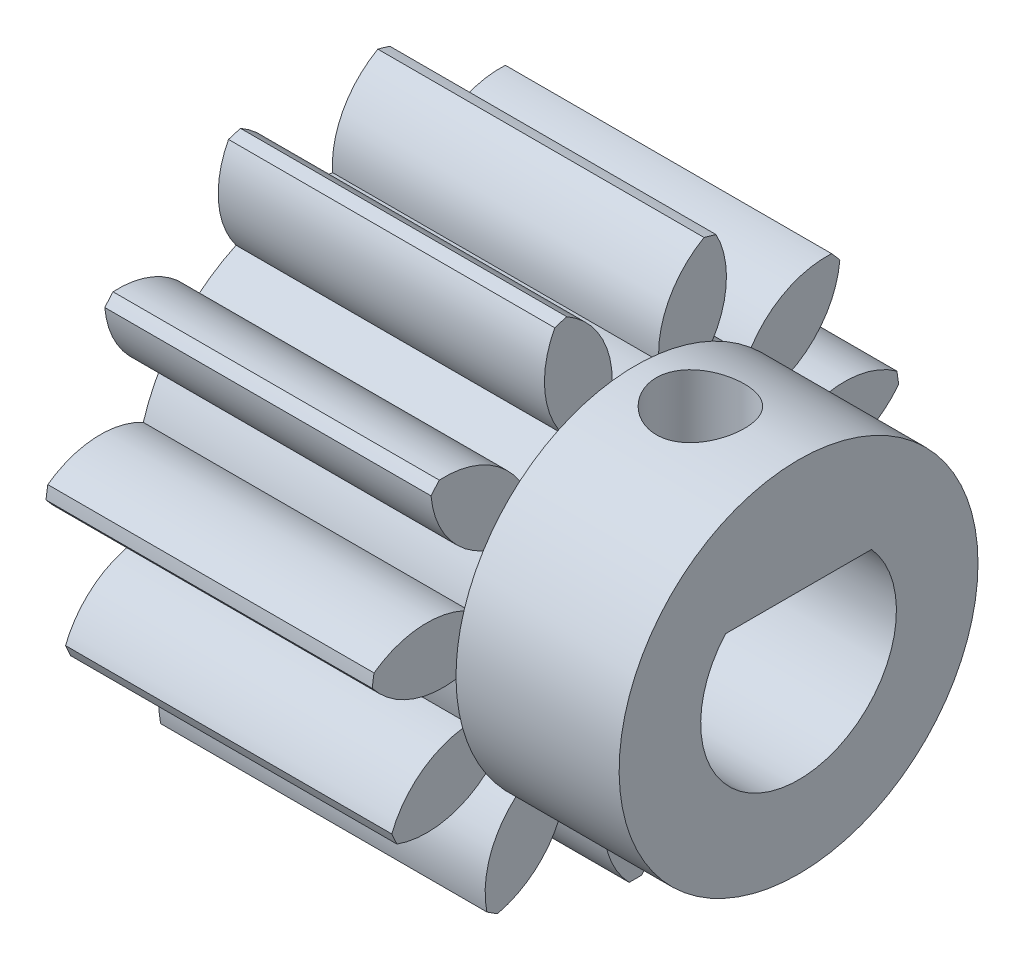
SolidWorks part; units mm, degrees
ref_plane "Plane1" through (0, 0, 0) normal (0, 0, 1) x (1, 0, 0)
ref_plane "Plane2" through (0, 0, 0) normal (0, 1, 0) x (1, 0, 0)
ref_plane "Plane3" through (0, 0, 0) normal (1, 0, 0) x (0, 0, -1)
sketch "HoldingSke" plane through (0, 0, 0) normal (0, 1, 0) x (1, 0, 0)
  line L0 (0, 0) -> (0.7853, -0.1526)
  line L1 (-15, 0) -> (100, 0) construction
  line L2 (0, 0) -> (-2.1039, 2.3779)
  line L3 (0, 0) -> (-11.863, 4.5341)
  line L4 (0, 0) -> (8.4773, 1.6478)
  line L5 (0, 0) -> (-46.8476, -17.4728)
  line L6 (0, 0) -> (-8.2896, -5.593)
  line L7 (-2.1039, 2.3779) -> (8.6586, 51.2059)
  line L8 (-76.2, 54.61) -> (-75.2, 54.61)
  line L9 (-71.009, 38.7566) -> (-53.1078, 45.2721)
  line L10 (-76.2, 71.12) -> (104.1128, 71.12)
  line L11 (0, 0) -> (-10, 0)
  line L12 (-76.2, 101.6) -> (-76.155, 101.6)
  line L13 (24.9733, 27.94) -> (52.9518, 28.4284)
  line L14 (24.9733, 27.94) -> (24.9743, 27.94)
  line L15 (24.9733, 27.94) -> (100.4006, 29.5858)
  line L16 (-63.627, -1.25) -> (-12.827, -1.25)
  circle A0 centre (0, 0) radius 3
  circle A1 centre (0, 0) radius 5.3115
  circle A2 centre (0, 0) radius 37.5
  circle A3 centre (0, 0) radius 3
  dimension "MHD" = 10.623
  dimension "Hub_dia" = 75
  dimension "Bore" = 6
  dimension "MBD" = 6
  dimension "Num_teeth" = 11
  dimension "Pitch" = 0.8
  dimension "Overall_len" = 50
  dimension "Show_teeth" = 11
  dimension "Thickness" = 10
  dimension "OAL" = 50.0001
  dimension "T_dim" = 1
  dimension "Ap" = 20
  dimension "H" = 19.05
  dimension "Pitch_radius" = 180.3128
  dimension "Width" = 10
  dimension "Backlash" = 0.045
  dimension "Addendum_fac" = 1
  dimension "Dedendum_fac" = 1.25
  dimension "Clearance_fac" = 0.25
  dimension "Dedendum_add" = 0.001
  dimension "Module" = 1.25
sketch "BasProSke" plane through (0, 0, 0) normal (0, 1, 0) x (1, 0, 0)
  line L0 (-10, 0) -> (60, 0) construction
  line L1 (0, 0) -> (0, 8.125)
  line L2 (0, 0) -> (10, 0)
  line L3 (10, 0) -> (10, 8.125)
  line L4 (10, 8.125) -> (0, 8.125)
  dimension "Thickness" = 10
  dimension "Diameter" = 16.25
revolve "Base-Revolve" add sketch "BasProSke" angle 360 about L0
sketch "TooCutSke" plane through (0, 0, 0) normal (1, 0, 0) x (0, 0, -1)
  line L1 (0, 0) -> (0, 107) construction
  line L2 (0, 0) -> (-1.057, 6.7933) construction
  line L3 (0, 0) -> (-3.8405, 13.0796) construction
  line L4 (-1.057, 6.7933) -> (-1.9203, 6.5398) construction
  arc A0 (0.7167, 5.2629) -> (-0.7167, 5.2629) centre (0, 0) ccw
  arc A1 (2.1352, 7.8657) -> (-2.1352, 7.8657) centre (0, 0) ccw
  circle A2 centre (0, 0) radius 6.875 construction
  circle A3 centre (0, 0) radius 6.4604 construction
  arc A4 (-0.7167, 5.2629) -> (-2.1352, 7.8657) centre (-3.4599, 5.4558) ccw
  arc A5 (2.1352, 7.8657) -> (0.7167, 5.2629) centre (3.4599, 5.4558) ccw
  dimension "Root_dia" = 10.623
  dimension "Overcut_dia" = 16.3008
  dimension "Pitch_dia" = 13.75
  dimension "Base_dia" = 12.9208
  dimension "Flank_rad" = 2.75
  dimension "Half_ang" = 16.364
  dimension "Half_CT" = 0.8997
extrude "ToothCut" cut sketch "TooCutSke" along normal through all
fillet "Breaks" [suppressed] radius 0.025
fillet "RootFillets" [suppressed] radius 0.3135
pattern_circular "TeethCuts" count 11 every 32.727 about axis through (-10, 0, 0) along (1, 0, 0) of "ToothCut", "RootFillets", "Breaks"
sketch "HubNeaOneSke" plane through (0, 0, 0) normal (-1, 0, 0) x (0, 0, 1)
  circle A0 centre (0, 0) radius 5.3115
  dimension "Diameter" = 10.623
extrude "HubNearOne" [suppressed] add sketch "HubNeaOneSke" along normal blind 40.0001
sketch "HubNeaBotSke" plane through (0, 0, 0) normal (-1, 0, 0) x (0, 0, 1)
  circle A0 centre (0, 0) radius 5.3115
  dimension "Diameter" = 10.623
extrude "HubNearBoth" [suppressed] add sketch "HubNeaBotSke" along normal blind 20
ref_plane "FarPln" through (10, 0, 0) normal (1, 0, 0) x (0, 0, -1)
sketch "HubFarSke" plane through (10, 0, 0) normal (1, 0, 0) x (0, 0, -1)
  circle A0 centre (0, 0) radius 5.3115
  dimension "Diameter" = 10.623
extrude "HubFar" [suppressed] add sketch "HubFarSke" along normal blind 20
sketch "BorSke" plane through (0, 0, 0) normal (1, 0, 0) x (0, 0, -1)
  circle A0 centre (0, 0) radius 3
  dimension "Diameter" = 6
extrude "Bore" cut sketch "BorSke" along normal mid plane 100.0001
sketch "KeySke" plane through (0, 0, 0) normal (1, 0, 0) x (0, 0, -1)
  line L0 (-1, 0) -> (-1, 4)
  line L1 (-1, 4) -> (1, 4)
  line L2 (1, 4) -> (1, 0)
  line L3 (0, 0) -> (0, 34) construction
  line L4 (-1, 0) -> (1, 0)
  dimension "Offset" = 4
  dimension "Width" = 2
extrude "Keyway" [suppressed] cut sketch "KeySke" along normal mid plane 100.0001
pattern_circular "Keyway2" [suppressed] count 2 every 90 about axis through (-10, 0, 0) along (1, 0, 0)
sketch "Esboço1" plane through (0, 0, 0) normal (-1, 0, 0) x (0, 0, 1)
  line L0 (0, 0) -> (0, 2) construction
  line L1 (0, 2) -> (-2.2361, 2)
  line L2 (-2.2361, 2) -> (2.2361, 2)
  circle A0 centre (0, 0) radius 3 construction
  arc A1 (2.2361, 2) -> (-2.2361, 2) centre (0, 0) ccw
  circle M1 centre (0, 0) radius 3
extrude "Ressalto-extrusão1" add sketch "Esboço1" against normal up to surface (10 mm away) contours L1 L2 M1
sketch "Esboço2" plane through (10, 0, 0) normal (1, 0, 0) x (0, 0, -1)
  line L0 (2.2361, 2) -> (-2.2361, 2) construction
  line L1 (2.2361, 2) -> (-2.2361, 2)
  circle A0 centre (0, 0) radius 5.5
  arc A44 (-7.3086, -3.5497) -> (-4.4468, -2.9049) centre (-6.389, -0.958) ccw
  arc A45 (-4.4468, -2.9049) -> (-3.5081, -3.9881) centre (0, 0) ccw
  arc A46 (-3.5081, -3.9881) -> (-4.5536, -6.729) centre (-1.8575, -6.1876) ccw
  arc A47 (-4.5536, -6.729) -> (-4.2293, -6.9375) centre (0, 0) ccw
  arc A48 (-4.2293, -6.9375) -> (-2.1704, -4.8478) centre (-4.8568, -4.26) ccw
  arc A49 (-2.1704, -4.8478) -> (-0.7951, -5.2517) centre (0, 0) ccw
  arc A50 (-0.7951, -5.2517) -> (-0.1928, -8.1227) centre (1.7827, -6.2096) ccw
  arc A51 (-0.1928, -8.1227) -> (0.1928, -8.1227) centre (0, 0) ccw
  arc A52 (0.1928, -8.1227) -> (0.7951, -5.2517) centre (-1.7827, -6.2096) ccw
  arc A53 (0.7951, -5.2517) -> (2.1704, -4.8478) centre (0, 0) ccw
  arc A54 (2.1704, -4.8478) -> (4.2293, -6.9375) centre (4.8568, -4.26) ccw
  arc A55 (4.2293, -6.9375) -> (4.5536, -6.729) centre (0, 0) ccw
  arc A56 (4.5536, -6.729) -> (3.5081, -3.9881) centre (1.8575, -6.1876) ccw
  arc A57 (3.5081, -3.9881) -> (4.4468, -2.9049) centre (0, 0) ccw
  arc A58 (4.4468, -2.9049) -> (7.3086, -3.5497) centre (6.389, -0.958) ccw
  arc A59 (7.3086, -3.5497) -> (7.4688, -3.1989) centre (0, 0) ccw
  arc A60 (7.4688, -3.1989) -> (5.1074, -1.4584) centre (4.9079, -4.2011) ccw
  arc A61 (5.1074, -1.4584) -> (5.3114, -0.0396) centre (0, 0) ccw
  arc A62 (5.3114, -0.0396) -> (8.0675, 0.9652) centre (5.8927, 2.6482) ccw
  arc A63 (8.0675, 0.9652) -> (8.0126, 1.3468) centre (0, 0) ccw
  arc A64 (8.0126, 1.3468) -> (5.085, 1.5344) centre (6.4001, -0.8808) ccw
  arc A65 (5.085, 1.5344) -> (4.4896, 2.8382) centre (0, 0) ccw
  arc A66 (4.4896, 2.8382) -> (6.265, 5.1736) centre (3.5255, 5.4136) ccw
  arc A67 (6.265, 5.1736) -> (6.0125, 5.4649) centre (0, 0) ccw
  arc A68 (6.0125, 5.4649) -> (3.4482, 4.04) centre (5.8603, 2.7192) ccw
  arc A69 (3.4482, 4.04) -> (2.2425, 4.8149) centre (0, 0) ccw
  arc A70 (2.2425, 4.8149) -> (2.4734, 7.7394) centre (0.039, 6.4603) ccw
  arc A71 (2.4734, 7.7394) -> (2.1035, 7.848) centre (0, 0) ccw
  arc A72 (2.1035, 7.848) -> (0.7167, 5.2629) centre (3.4599, 5.4558) ccw
  arc A73 (0.7167, 5.2629) -> (-0.7167, 5.2629) centre (0, 0) ccw
  arc A74 (-0.7167, 5.2629) -> (-2.1035, 7.848) centre (-3.4599, 5.4558) ccw
  arc A75 (-2.1035, 7.848) -> (-2.4734, 7.7394) centre (0, 0) ccw
  arc A76 (-2.4734, 7.7394) -> (-2.2425, 4.8149) centre (-0.039, 6.4603) ccw
  arc A77 (-2.2425, 4.8149) -> (-3.4482, 4.04) centre (0, 0) ccw
  arc A78 (-3.4482, 4.04) -> (-6.0125, 5.4649) centre (-5.8603, 2.7192) ccw
  arc A79 (-6.0125, 5.4649) -> (-6.265, 5.1736) centre (0, 0) ccw
  arc A80 (-6.265, 5.1736) -> (-4.4896, 2.8382) centre (-3.5255, 5.4136) ccw
  arc A81 (-4.4896, 2.8382) -> (-5.085, 1.5344) centre (0, 0) ccw
  arc A82 (-5.085, 1.5344) -> (-8.0126, 1.3468) centre (-6.4001, -0.8808) ccw
  arc A83 (-8.0126, 1.3468) -> (-8.0675, 0.9652) centre (0, 0) ccw
  arc A84 (-8.0675, 0.9652) -> (-5.3114, -0.0396) centre (-5.8927, 2.6482) ccw
  arc A85 (-5.3114, -0.0396) -> (-5.1074, -1.4584) centre (0, 0) ccw
  arc A86 (-5.1074, -1.4584) -> (-7.4688, -3.1989) centre (-4.9079, -4.2011) ccw
  arc A87 (-7.4688, -3.1989) -> (-7.3086, -3.5497) centre (0, 0) ccw
  arc A88 (-7.3086, -3.5497) -> (-4.4468, -2.9049) centre (-6.389, -0.958) ccw
  arc A89 (-4.4468, -2.9049) -> (-3.5081, -3.9881) centre (0, 0) ccw
  arc A90 (-3.5081, -3.9881) -> (-4.5536, -6.729) centre (-1.8575, -6.1876) ccw
  arc A91 (-4.5536, -6.729) -> (-4.2293, -6.9375) centre (0, 0) ccw
  arc A92 (-4.2293, -6.9375) -> (-2.1704, -4.8478) centre (-4.8568, -4.26) ccw
  arc A93 (-2.1704, -4.8478) -> (-0.7951, -5.2517) centre (0, 0) ccw
  arc A94 (-0.7951, -5.2517) -> (-0.1928, -8.1227) centre (1.7827, -6.2096) ccw
  arc A95 (-0.1928, -8.1227) -> (0.1928, -8.1227) centre (0, 0) ccw
  arc A96 (0.1928, -8.1227) -> (0.7951, -5.2517) centre (-1.7827, -6.2096) ccw
  arc A97 (0.7951, -5.2517) -> (2.1704, -4.8478) centre (0, 0) ccw
  arc A98 (2.1704, -4.8478) -> (4.2293, -6.9375) centre (4.8568, -4.26) ccw
  arc A99 (4.2293, -6.9375) -> (4.5536, -6.729) centre (0, 0) ccw
  arc A100 (4.5536, -6.729) -> (3.5081, -3.9881) centre (1.8575, -6.1876) ccw
  arc A101 (3.5081, -3.9881) -> (4.4468, -2.9049) centre (0, 0) ccw
  arc A102 (4.4468, -2.9049) -> (7.3086, -3.5497) centre (6.389, -0.958) ccw
  arc A103 (7.3086, -3.5497) -> (7.4688, -3.1989) centre (0, 0) ccw
  arc A104 (7.4688, -3.1989) -> (5.1074, -1.4584) centre (4.9079, -4.2011) ccw
  arc A105 (5.1074, -1.4584) -> (5.3114, -0.0396) centre (0, 0) ccw
  arc A106 (5.3114, -0.0396) -> (8.0675, 0.9652) centre (5.8927, 2.6482) ccw
  arc A107 (8.0675, 0.9652) -> (8.0126, 1.3468) centre (0, 0) ccw
  arc A108 (8.0126, 1.3468) -> (5.085, 1.5344) centre (6.4001, -0.8808) ccw
  arc A109 (5.085, 1.5344) -> (4.4896, 2.8382) centre (0, 0) ccw
  arc A110 (4.4896, 2.8382) -> (6.265, 5.1736) centre (3.5255, 5.4136) ccw
  arc A111 (6.265, 5.1736) -> (6.0125, 5.4649) centre (0, 0) ccw
  arc A112 (6.0125, 5.4649) -> (3.4482, 4.04) centre (5.8603, 2.7192) ccw
  arc A113 (3.4482, 4.04) -> (2.2425, 4.8149) centre (0, 0) ccw
  arc A114 (2.2425, 4.8149) -> (2.4734, 7.7394) centre (0.039, 6.4603) ccw
  arc A115 (2.4734, 7.7394) -> (2.1035, 7.848) centre (0, 0) ccw
  arc A116 (2.1035, 7.848) -> (0.7167, 5.2629) centre (3.4599, 5.4558) ccw
  arc A117 (0.7167, 5.2629) -> (-0.7167, 5.2629) centre (0, 0) ccw
  arc A118 (-0.7167, 5.2629) -> (-2.1035, 7.848) centre (-3.4599, 5.4558) ccw
  arc A119 (-2.1035, 7.848) -> (-2.4734, 7.7394) centre (0, 0) ccw
  arc A120 (-2.4734, 7.7394) -> (-2.2425, 4.8149) centre (-0.039, 6.4603) ccw
  arc A121 (-2.2425, 4.8149) -> (-3.4482, 4.04) centre (0, 0) ccw
  arc A122 (-3.4482, 4.04) -> (-6.0125, 5.4649) centre (-5.8603, 2.7192) ccw
  arc A123 (-6.0125, 5.4649) -> (-6.265, 5.1736) centre (0, 0) ccw
  arc A124 (-6.265, 5.1736) -> (-4.4896, 2.8382) centre (-3.5255, 5.4136) ccw
  arc A125 (-4.4896, 2.8382) -> (-5.085, 1.5344) centre (0, 0) ccw
  arc A126 (-5.085, 1.5344) -> (-8.0126, 1.3468) centre (-6.4001, -0.8808) ccw
  arc A127 (-8.0126, 1.3468) -> (-8.0675, 0.9652) centre (0, 0) ccw
  arc A128 (-8.0675, 0.9652) -> (-5.3114, -0.0396) centre (-5.8927, 2.6482) ccw
  arc A129 (-5.3114, -0.0396) -> (-5.1074, -1.4584) centre (0, 0) ccw
  arc A130 (-5.1074, -1.4584) -> (-7.4688, -3.1989) centre (-4.9079, -4.2011) ccw
  arc A131 (-7.4688, -3.1989) -> (-7.3086, -3.5497) centre (0, 0) ccw
  arc M45 (2.2361, 2) -> (-2.2361, 2) centre (0, 0) cw
  line M46 (-2.2361, 2) -> (2.2361, 2)
  arc M47 (-7.3086, -3.5497) -> (-4.4468, -2.9049) centre (-6.389, -0.958) ccw
  arc M48 (-4.4468, -2.9049) -> (-3.5081, -3.9881) centre (0, 0) ccw
  arc M49 (-3.5081, -3.9881) -> (-4.5536, -6.729) centre (-1.8575, -6.1876) ccw
  arc M51 (-4.2293, -6.9375) -> (-2.1704, -4.8478) centre (-4.8568, -4.26) ccw
  arc M52 (-2.1704, -4.8478) -> (-0.7951, -5.2517) centre (0, 0) ccw
  arc M53 (-0.7951, -5.2517) -> (-0.1928, -8.1227) centre (1.7827, -6.2096) ccw
  arc M55 (0.1928, -8.1227) -> (0.7951, -5.2517) centre (-1.7827, -6.2096) ccw
  arc M56 (0.7951, -5.2517) -> (2.1704, -4.8478) centre (0, 0) ccw
  arc M57 (2.1704, -4.8478) -> (4.2293, -6.9375) centre (4.8568, -4.26) ccw
  arc M59 (4.5536, -6.729) -> (3.5081, -3.9881) centre (1.8575, -6.1876) ccw
  arc M60 (3.5081, -3.9881) -> (4.4468, -2.9049) centre (0, 0) ccw
  arc M61 (4.4468, -2.9049) -> (7.3086, -3.5497) centre (6.389, -0.958) ccw
  arc M63 (7.4688, -3.1989) -> (5.1074, -1.4584) centre (4.9079, -4.2011) ccw
  arc M64 (5.1074, -1.4584) -> (5.3114, -0.0396) centre (0, 0) ccw
  arc M65 (5.3114, -0.0396) -> (8.0675, 0.9652) centre (5.8927, 2.6482) ccw
  arc M67 (8.0126, 1.3468) -> (5.085, 1.5344) centre (6.4001, -0.8808) ccw
  arc M68 (5.085, 1.5344) -> (4.4896, 2.8382) centre (0, 0) ccw
  arc M69 (4.4896, 2.8382) -> (6.265, 5.1736) centre (3.5255, 5.4136) ccw
  arc M71 (6.0125, 5.4649) -> (3.4482, 4.04) centre (5.8603, 2.7192) ccw
  arc M72 (3.4482, 4.04) -> (2.2425, 4.8149) centre (0, 0) ccw
  arc M73 (2.2425, 4.8149) -> (2.4734, 7.7394) centre (0.039, 6.4603) ccw
  arc M75 (2.1035, 7.848) -> (0.7167, 5.2629) centre (3.4599, 5.4558) ccw
  arc M76 (0.7167, 5.2629) -> (-0.7167, 5.2629) centre (0, 0) ccw
  arc M77 (-0.7167, 5.2629) -> (-2.1035, 7.848) centre (-3.4599, 5.4558) ccw
  arc M79 (-2.4734, 7.7394) -> (-2.2425, 4.8149) centre (-0.039, 6.4603) ccw
  arc M80 (-2.2425, 4.8149) -> (-3.4482, 4.04) centre (0, 0) ccw
  arc M81 (-3.4482, 4.04) -> (-6.0125, 5.4649) centre (-5.8603, 2.7192) ccw
  arc M83 (-6.265, 5.1736) -> (-4.4896, 2.8382) centre (-3.5255, 5.4136) ccw
  arc M84 (-4.4896, 2.8382) -> (-5.085, 1.5344) centre (0, 0) ccw
  arc M85 (-5.085, 1.5344) -> (-8.0126, 1.3468) centre (-6.4001, -0.8808) ccw
  arc M87 (-8.0675, 0.9652) -> (-5.3114, -0.0396) centre (-5.8927, 2.6482) ccw
  arc M88 (-5.3114, -0.0396) -> (-5.1074, -1.4584) centre (0, 0) ccw
  arc M89 (-5.1074, -1.4584) -> (-7.4688, -3.1989) centre (-4.9079, -4.2011) ccw
  dimension "D1" = 0
extrude "Ressalto-extrusão2" add sketch "Esboço2" along normal blind 5 contours A0 M69 M71 M72 M73 M75 M76 M77 M79 M80 M81 M83 M84 M85 M87 M88 M89 M47 M48 M49 M51 M52 M53 M55 M56 M57 M59 M60 M61 M63 M64 M65 M67 M68 M46 M45 | A0 M71 M73 M72 | A0 M75 M77 M76 | A0 M79 M81 M80 | A0 M83 M85 M84 | A0 M87 M89 M88 | A0 M47 M49 M48 | A0 M51 M53 M52 | A0 M55 M57 M56 | A0 M59 M61 M60 | A0 M63 M65 M64 | A0 M67 M69 M68
sketch "Esboço3" plane through (0, 2, 0) normal (0, -1, 0) x (1, 0, 0)
  line L0 (15, 0) -> (-4.5752, 0) construction
  line L1 (15, -5.5) -> (15, 5.5) construction
  circle A0 centre (11.9907, 0) radius 1.35
  point P10 (0, 0)
  dimension "D1" = 2
extrude "Corte-extrusão1" cut sketch "Esboço3" against normal blind 10
equation "' \"Module@HoldingSke\" = 6.35"
equation "' \"Num_teeth@HoldingSke\" = 12"
equation "' \"Ap@HoldingSke\" =  20"
equation "' \"Ap@HoldingSke\" = 20"
equation "' \"Width@HoldingSke\" = 0.5 * 25.4"
equation "' \"Hub_dia@HoldingSke\"= 1 * 25.4"
equation "' \"Hub_dia@HoldingSke\" = 1 * 25.4"
equation "' \"Overall_len@HoldingSke\" = 1.0 * 25.4"
equation "' \"Bore@HoldingSke\" = 0.75 * 25.4"
equation "' \"T_dim@HoldingSke\" = 0.1 * 25.4"
equation "' \"Width@KeySke\" = 0.25 * 25.4"
equation "' \"Show_teeth@HoldingSke\" = 13"
equation "' \"Backlash@HoldingSke\" = 0.009 * 25.4"
equation "' \"Addendum_fac@HoldingSke\" = 1.0"
equation "' \"Dedendum_fac@HoldingSke\" = 1.25"
equation "' \"Dedendum_add@HoldingSke\" = 0.00005 * 25.4"
equation "' \"Clearance_fac@HoldingSke\" = 0.25"
equation "\"Pitch@HoldingSke\" = 1 / \"Module@HoldingSke\""
equation "\"Overcut_dia@TooCutSke\" = (\"Num_teeth@HoldingSke\" + 2 * \"Addendum_fac@HoldingSke\") / \"Pitch@HoldingSke\" + 0.002 * 25.4"
equation "\"Pitch_dia@TooCutSke\" = \"Num_teeth@HoldingSke\" / \"Pitch@HoldingSke\""
equation "\"Base_dia@TooCutSke\" = \"Num_teeth@HoldingSke\" / \"Pitch@HoldingSke\" * cos((\"Ap@HoldingSke\"  * 3.14159265 / 180))"
equation "\"Root_dia@TooCutSke\" = (\"Num_teeth@HoldingSke\" + 2) / \"Pitch@HoldingSke\" - 2 * (\"Addendum_fac@HoldingSke\" + \"Dedendum_fac@HoldingSke\") / \"Pitch@HoldingSke\" - \"Dedendum_add@HoldingSke\" * 2"
equation "\"Half_ang@TooCutSke\" = 180 / \"Num_teeth@HoldingSke\""
equation "\"Half_CT@TooCutSke\" = \"Num_teeth@HoldingSke\" / \"Pitch@HoldingSke\" * sin((3.14159265 / 2 / \"Num_teeth@HoldingSke\")) / 2 - 7 * \"Backlash@HoldingSke\" / 4"
equation "\"Flank_rad@TooCutSke\" = \"Num_teeth@HoldingSke\" / \"Pitch@HoldingSke\" / 5"
equation "\"Radius@RootFillets\" = \"Clearance_fac@HoldingSke\" / \"Pitch@HoldingSke\" + \"Dedendum_add@HoldingSke\""
equation "\"Break_rad@Breaks\" = 0.02 / \"Pitch@HoldingSke\""
equation "\"Thickness@HoldingSke\" = \"Width@HoldingSke\""
equation "\"OAL@HoldingSke\" = \"Thickness@HoldingSke\""
equation "\"MHD@HoldingSke\" = (\"Num_teeth@HoldingSke\" + 2) / \"Pitch@HoldingSke\" - 2 * (\"Addendum_fac@HoldingSke\" + \"Dedendum_fac@HoldingSke\")  / \"Pitch@HoldingSke\" - \"Dedendum_add@HoldingSke\" * 2"
equation "\"MBD@HoldingSke\" = (\"Num_teeth@HoldingSke\" + 2) / \"Pitch@HoldingSke\" - 2 * (\"Addendum_fac@HoldingSke\" + \"Dedendum_fac@HoldingSke\")  / \"Pitch@HoldingSke\" - \"Dedendum_add@HoldingSke\" * 2 - 0.002 * 25.4"
equation "\"MHD@HoldingSke\" = ((sgn( \"MHD@HoldingSke\" - \"Hub_dia@HoldingSke\" )-1)*( \"MHD@HoldingSke\" - \"Hub_dia@HoldingSke\" ))/-2+ \"Hub_dia@HoldingSke\""
equation "\"MBD@HoldingSke\" = ((sgn( \"MBD@HoldingSke\" - \"Bore@HoldingSke\" )-1)*( \"MBD@HoldingSke\" - \"Bore@HoldingSke\" ))/-2+ \"Bore@HoldingSke\""
equation "\"OAL@HoldingSke\" = ((sgn( \"OAL@HoldingSke\" - \"Overall_len@HoldingSke\" )+1)*( \"OAL@HoldingSke\" - \"Overall_len@HoldingSke\" ))/2 + \"Overall_len@HoldingSke\" + 0.000002 * 25.4"
equation "\"Num_teeth@TeethCuts\" = int( \"Show_teeth@HoldingSke\" ) + 1"
equation "\"Num_teeth@TeethCuts\" = ((sgn( \"Num_teeth@TeethCuts\" - \"Num_teeth@HoldingSke\" )-1)*( \"Num_teeth@TeethCuts\" - \"Num_teeth@HoldingSke\" ))/-2+ \"Num_teeth@HoldingSke\""
equation "\"Num_teeth@TeethCuts\" = ((sgn( \"Num_teeth@TeethCuts\" - 2.0)+1)*( \"Num_teeth@TeethCuts\" - 2.0))/2 +2.0"
equation "\"Angle@TeethCuts\" = 360.0 / \"Num_teeth@HoldingSke\""
equation "\"Diameter@BasProSke\" = (\"Num_teeth@HoldingSke\" + 2 * \"Addendum_fac@HoldingSke\") / \"Pitch@HoldingSke\""
equation "\"Thickness@BasProSke\"  = \"Thickness@HoldingSke\""
equation "' \"Fillet_rad@BasProSke\" =  \"Thickness@HoldingSke\" * 0.05"
equation "' \"Fillet_rad@BasProSke\" = \"Thickness@HoldingSke\" * 0.05"
equation "\"MHD@HoldingSke\" = ((sgn( \"MHD@HoldingSke\" - \"Root_dia@TooCutSke\" )-1)*( \"MHD@HoldingSke\" - \"Root_dia@TooCutSke\" ))/-2+ \"Root_dia@TooCutSke\""
equation "\"Diameter@HubNeaOneSke\" = \"MHD@HoldingSke\""
equation "\"Length@HubNearOne\" = \"OAL@HoldingSke\" - \"Thickness@BasProSke\""
equation "\"Diameter@HubNeaBotSke\" = \"MHD@HoldingSke\""
equation "\"Length@HubNearBoth\" = ( \"OAL@HoldingSke\" - \"Thickness@BasProSke\" ) / 2.0"
equation "\"Thickness@FarPln\" = \"Thickness@BasProSke\""
equation "\"Diameter@HubFarSke\" = \"MHD@HoldingSke\""
equation "\"Length@HubFar\" = ( \"OAL@HoldingSke\" - \"Thickness@BasProSke\" ) / 2.0"
equation "\"Diameter@BorSke\" = \"MBD@HoldingSke\""
equation "\"D1@Bore\" = \"OAL@HoldingSke\" * 2.0"
equation "\"D1@Keyway\" = \"OAL@HoldingSke\" * 2.0"
equation "\"Offset@KeySke\" = \"T_dim@HoldingSke\" + \"MBD@HoldingSke\" / 2.0"
